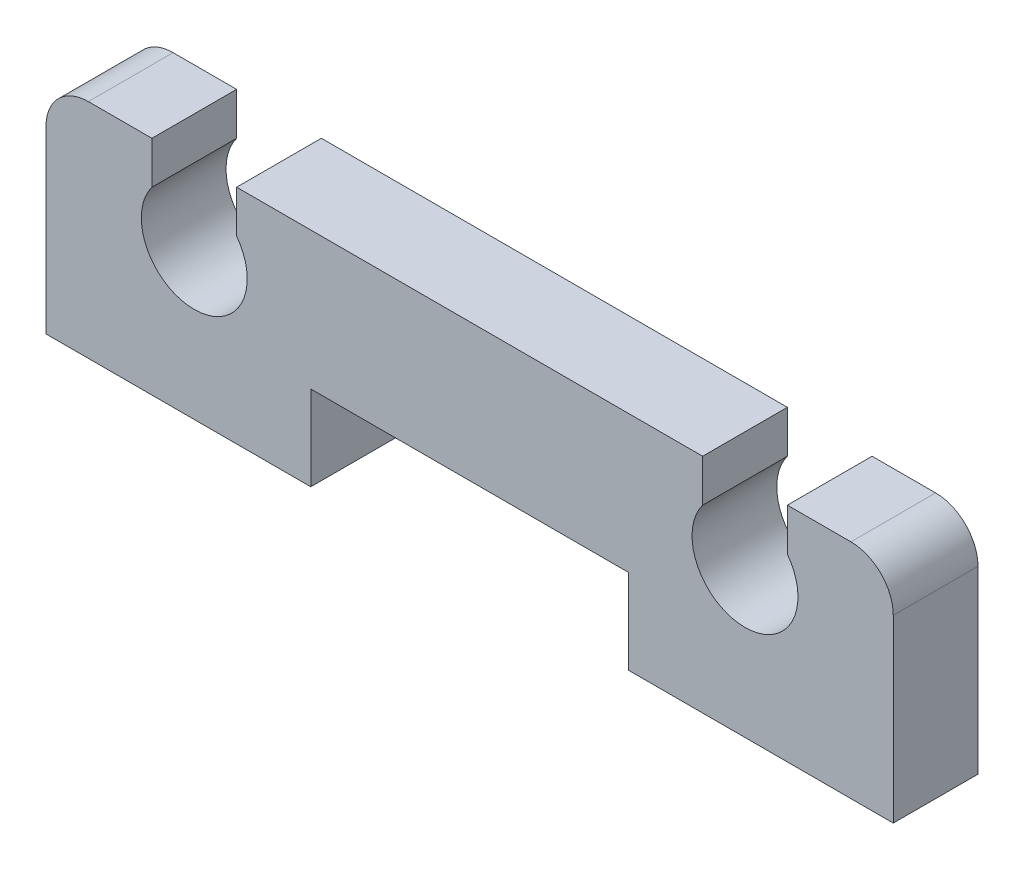
SolidWorks part; units mm, degrees
ref_plane "Front Plane" through (0, 0, 0) normal (0, 0, 1) x (1, 0, 0)
ref_plane "Top Plane" through (0, 0, 0) normal (0, 1, 0) x (1, 0, 0)
ref_plane "Right Plane" through (0, 0, 0) normal (1, 0, 0) x (0, 0, -1)
sketch "Sketch1" plane through (0, 0, 0) normal (0, 0, 1) x (1, 0, 0)
  line L14 (-10, 0) -> (-10, 5.25)
  line L15 (-10, 5.25) -> (-7.5, 5.25)
  line L16 (-10, 0) -> (-3.75, 0)
  line L17 (-3.75, 0) -> (-3.75, 2)
  line L18 (-3.75, 2) -> (3.75, 2)
  line L19 (0, 5.25) -> (0, 0) construction
  line L20 (-7.5, 4.25) -> (-7.5, 5.25)
  line L21 (-5.5, 4.25) -> (-5.5, 5.25)
  line L22 (-5.5, 5.25) -> (5.5, 5.25)
  line L23 (5.5, 4.25) -> (5.5, 5.25)
  line L24 (7.5, 4.25) -> (7.5, 5.25)
  line L25 (3.75, 0) -> (3.75, 2)
  line L26 (10, 0) -> (3.75, 0)
  line L27 (10, 5.25) -> (7.5, 5.25)
  line L28 (10, 0) -> (10, 5.25)
  arc A4 (-7.5, 4.25) -> (-5.5, 4.25) centre (-6.5, 3.5) ccw
  arc A5 (7.5, 4.25) -> (5.5, 4.25) centre (6.5, 3.5) cw
  point P41 (0, 2)
  dimension "D2" = 10
  dimension "D10" = 1.25
  dimension "D3" = 2
  dimension "D4" = 1.75
  dimension "D5" = 2
  dimension "D6" = 5.25
  dimension "D7" = 6.25
  dimension "D9" = 3.5
extrude "Tube Plate Body" add sketch "Sketch1" along normal blind 2
fillet "Tube Plate Contouring" radius 1 2 edges at (10, 5.25, 1) (-10, 5.25, 1)
equation "\"D2@Sketch1\"=\"Wph@Parameters@RobotHandParameters.SLDPRT\"/2"
equation "\"D6@Sketch1\"=\"rd@Parameters@RobotHandParameters.SLDPRT\" - 2 - \"Tjointd@Parameters@RobotHandParameters.SLDPRT\"/2 + 1.75"
